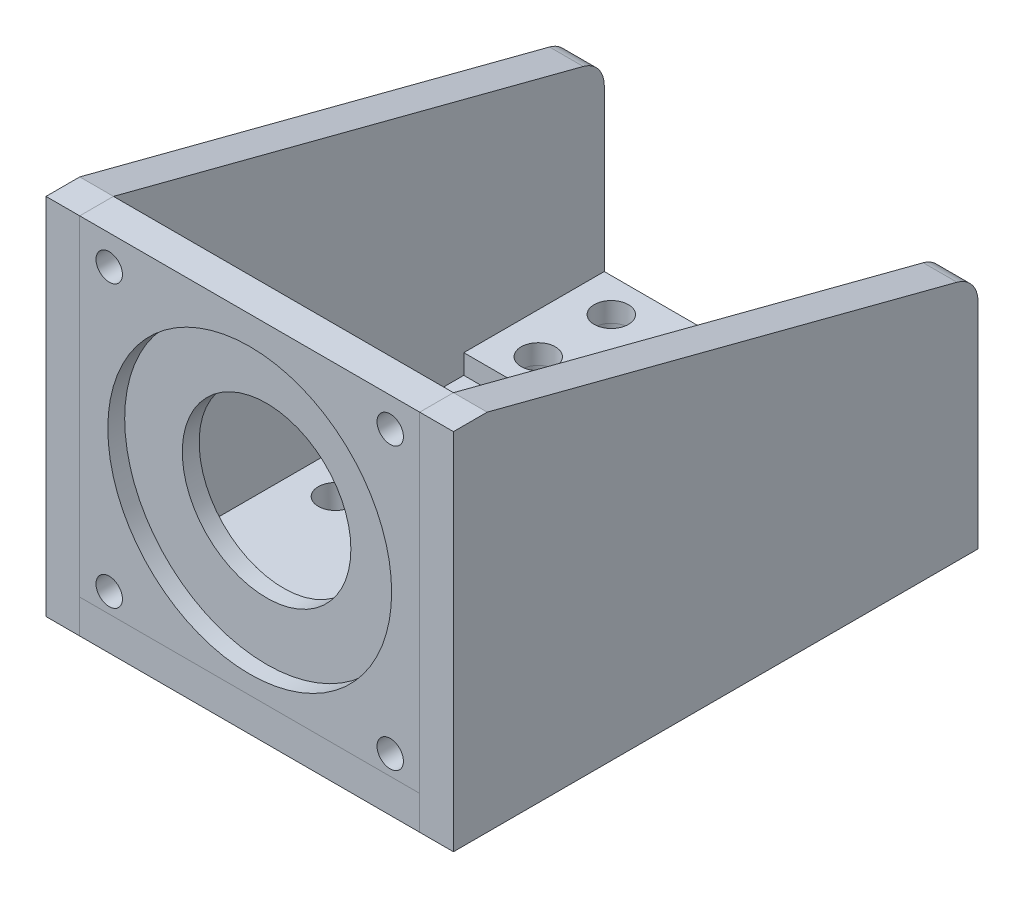
SolidWorks part; units mm, degrees
ref_plane "Front Plane" through (0, 0, 0) normal (0, 0, 1) x (1, 0, 0)
ref_plane "Top Plane" through (0, 0, 0) normal (0, 1, 0) x (1, 0, 0)
ref_plane "Right Plane" through (0, 0, 0) normal (1, 0, 0) x (0, 0, -1)
sketch "Sketch1" plane through (0, 0, 0) normal (0, 0, 1) x (1, 0, 0)
  line L1 (-30.25, -30.25) -> (30.25, -30.25)
  line L2 (-30.25, -30.25) -> (-30.25, 30.25)
  line L3 (-30.25, 30.25) -> (30.25, 30.25)
  line L4 (30.25, -30.25) -> (30.25, 30.25)
  line L5 (-30.25, -30.25) -> (30.25, 30.25) construction
  line L6 (-30.25, 30.25) -> (30.25, -30.25) construction
  line L7 (25, -25) -> (-25, -25) construction
  line L8 (25, -25) -> (25, 25) construction
  line L9 (25, 25) -> (-25, 25) construction
  line L10 (-25, -25) -> (-25, 25) construction
  line L11 (25, -25) -> (-25, 25) construction
  line L12 (25, 25) -> (-25, -25) construction
  circle A0 centre (0, 0) radius 15
  circle A1 centre (-25, 25) radius 2.35
  circle A2 centre (25, 25) radius 2.35
  circle A3 centre (25, -25) radius 2.35
  circle A4 centre (-25, -25) radius 2.35
  point P0 (0, 0)
  dimension "D2" = 4.7
  dimension "D4" = 30
  dimension "D1" = 60.5
  dimension "D3" = 50
extrude "Boss-Extrude1" add sketch "Sketch1" against normal blind 6
sketch "Sketch2" plane through (0, 0, 0) normal (0, 0, 1) x (1, 0, 0)
  circle A0 centre (0, 0) radius 25.25
  dimension "D1" = 50.5
extrude "Cut-Extrude1" cut sketch "Sketch2" against normal blind 3
sketch "Sketch3" plane through (0, -30.25, 0) normal (0, -1, 0) x (1, 0, 0)
  line L4 (30.25, 0) -> (-30.25, 0)
  line L5 (-30.25, 0) -> (-30.25, -6)
  line L6 (-30.25, -6) -> (30.25, -6)
  line L7 (30.25, -6) -> (30.25, 0)
  line L8 (30.25, 0) -> (-30.25, 0)
  line L9 (-30.25, 0) -> (-30.25, -6)
  line L10 (-30.25, -6) -> (30.25, -6)
  line L11 (30.25, -6) -> (30.25, 0)
  dimension "D1" = 0
extrude "Boss-Extrude2" add sketch "Sketch3" along normal blind 4.25
sketch "Sketch4" plane through (0, 0, -6) normal (0, 0, -1) x (-1, 0, 0)
  line L0 (30.25, 30.25) -> (30.25, -34.5) construction
  line L1 (-30.25, -34.5) -> (30.25, -34.5)
  line L2 (-30.25, -34.5) -> (-30.25, -28.5)
  line L3 (-30.25, -28.5) -> (30.25, -28.5)
  line L4 (30.25, -34.5) -> (30.25, -28.5)
  dimension "D1" = 6
extrude "Boss-Extrude3" add sketch "Sketch4" along normal blind 87.34
sketch "Sketch5" plane through (30.25, 0, 0) normal (1, 0, 0) x (0, 0, -1)
  line L0 (0, 30.25) -> (6, 30.25)
  line L1 (6, 30.25) -> (93.34, 7.5)
  line L2 (93.34, 7.5) -> (93.34, -34.5)
  line L3 (93.34, -34.5) -> (0, -34.5)
  line L4 (0, -34.5) -> (0, 30.25)
  dimension "D1" = 42
extrude "Boss-Extrude4" add sketch "Sketch5" along normal blind 6
mirror "Mirror1" about plane through (0, 0, 0) normal (1, 0, 0) of "Boss-Extrude4"
sketch "Sketch6" plane through (0, -28.5, 0) normal (0, 1, 0) x (1, 0, 0)
  line L0 (30.25, 93.34) -> (30.25, 6) construction
  line L1 (-30.25, 93.34) -> (30.25, 93.34)
  line L2 (-30.25, 93.34) -> (-30.25, 68.34)
  line L3 (-30.25, 68.34) -> (30.25, 68.34)
  line L4 (30.25, 93.34) -> (30.25, 68.34)
  dimension "D1" = 25
extrude "Boss-Extrude5" add sketch "Sketch6" along normal blind 3.5
sketch "Sketch7" plane through (0, -25, 0) normal (0, 1, 0) x (1, 0, 0)
  line L0 (0, 80.84) -> (0, 93.34) construction
  line L1 (23, 74.34) -> (-23, 74.34) construction
  line L2 (23, 74.34) -> (23, 87.34) construction
  line L3 (23, 87.34) -> (-23, 87.34) construction
  line L4 (-23, 74.34) -> (-23, 87.34) construction
  line L5 (23, 74.34) -> (-23, 87.34) construction
  line L6 (23, 87.34) -> (-23, 74.34) construction
  line L7 (30.25, 93.34) -> (-30.25, 93.34) construction
  line L8 (-23, 13.25) -> (-23, 6) construction
  line L9 (-23, 74.34) -> (23, 74.34) construction
  line L10 (-23, 74.34) -> (-23, 13.25) construction
  line L11 (-23, 13.25) -> (23, 13.25) construction
  line L12 (23, 74.34) -> (23, 13.25) construction
  line L13 (-30.25, 6) -> (30.25, 6) construction
  line L14 (-23, 13.25) -> (-30.25, 13.25) construction
  line L15 (-30.25, 68.34) -> (-30.25, 6) construction
  line L16 (-23, 38.25) -> (23, 38.25) construction
  circle A0 centre (-23, 87.34) radius 3.05
  circle A1 centre (23, 87.34) radius 3.05
  circle A2 centre (23, 74.34) radius 3.05
  circle A3 centre (-23, 74.34) radius 3.05
  circle A4 centre (-23, 13.25) radius 3.05
  circle A5 centre (23, 13.25) radius 3.05
  circle A6 centre (-23, 38.25) radius 3.05
  circle A7 centre (23, 38.25) radius 3.05
  point P0 (23, 87.34)
  point P1 (23, 74.34)
  point P3 (-23, 74.34)
  point P5 (-23, 87.34)
  point P7 (0, 80.84)
  dimension "D4" = 6.1
  dimension "D1" = 46
  dimension "D2" = 13
  dimension "D3" = 6
  dimension "D5" = 25
extrude "Cut-Extrude2" cut sketch "Sketch7" against normal through all both and the other way through all
fillet "Fillet1" radius 5 2 edges at (-33.25, 7.5, -93.34) (33.25, 7.5, -93.34)
sketch "Sketch8" plane through (0, 30.25, 0) normal (0, 1, 0) x (1, 0, 0)
  line L0 (-30.25, 93.34) -> (-30.25, 0)
  line L1 (36.25, 0) -> (-36.25, 0) construction
  line L2 (30.25, 93.34) -> (30.25, 0)
split "Split1" trim tools "Sketch8" bodies to split 108 resulting bodies 109 110 111
sketch "Sketch9" plane through (30.25, 0, 0) normal (1, 0, 0) x (0, 0, -1)
  line L0 (0, -28.5) -> (93.34, -28.5)
  line L1 (0, -34.5) -> (0, 30.25) construction
  line L2 (93.34, -25) -> (93.34, -34.5) construction
  line L3 (68.34, -28.5) -> (6, -28.5) construction
split "Split2" trim tools "Sketch9" bodies to split 109 resulting bodies 112 113 114
